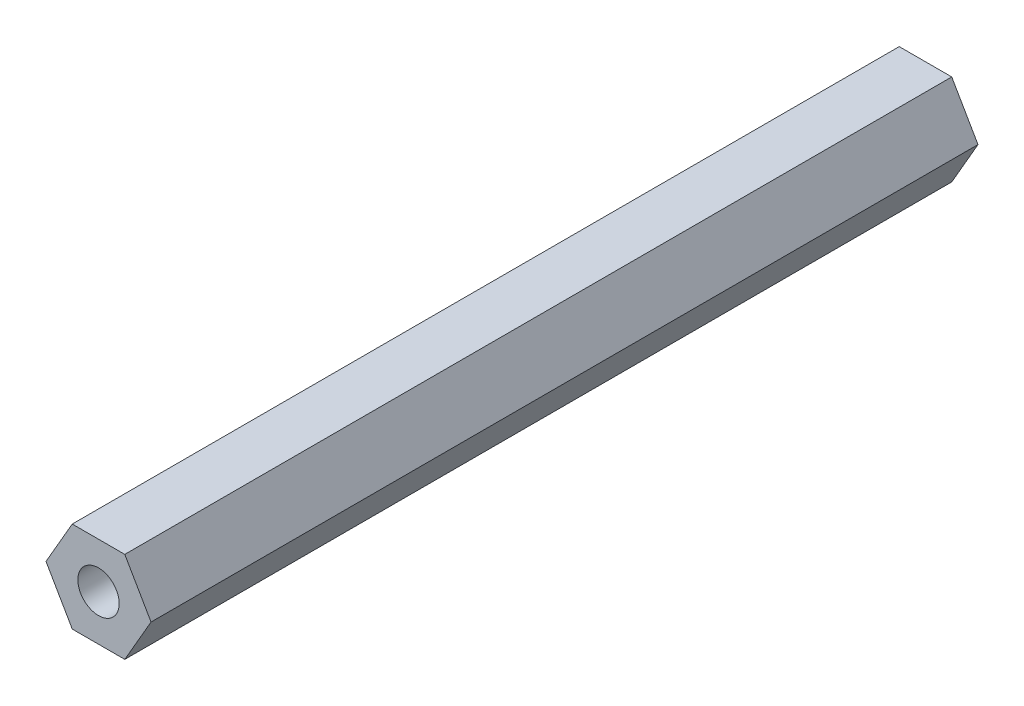
SolidWorks part; units mm, degrees
ref_plane "Front Plane" through (0, 0, 0) normal (0, 0, 1) x (1, 0, 0)
ref_plane "Top Plane" through (0, 0, 0) normal (0, 1, 0) x (1, 0, 0)
ref_plane "Right Plane" through (0, 0, 0) normal (1, 0, 0) x (0, 0, -1)
sketch "Sketch1" plane through (0, 0, 0) normal (0, 0, 1) x (1, 0, 0)
  line L1 (3.1754, 0) -> (1.5877, 2.75)
  line L2 (1.5877, 2.75) -> (-1.5877, 2.75)
  line L3 (-1.5877, 2.75) -> (-3.1754, 0)
  line L4 (-3.1754, 0) -> (-1.5877, -2.75)
  line L5 (-1.5877, -2.75) -> (1.5877, -2.75)
  line L6 (1.5877, -2.75) -> (3.1754, 0)
  circle A0 centre (0, 0) radius 2.75 construction
  dimension "D1" = 5.5
extrude "Boss-Extrude1" add sketch "Sketch1" along normal blind 50
sketch "Sketch3" plane through (0, 0, 50) normal (0, 0, 1) x (1, 0, 0)
  circle A0 centre (0, 0) radius 1.3122
hole_wizard "M3x0.5 Tapped Hole1" positions "3DSketch2" profile "Sketch4" tap size "M3x0.5" standard "ANSI Metric" end condition through all
sketch3d "3DSketch2"
  point P0 (0, 0, 50)
sketch "Sketch4" plane through (0, 0, 50) normal (1, 0, 0) x (0, -1, 0)
  line L0 (0, 0) -> (0, 50)
  line L1 (0, 50) -> (1.25, 50)
  line L2 (1.25, 50) -> (1.25, 0)
  line L5 (1.25, 0) -> (0, 0)
  line L11 (0, -6.35) -> (0, 107.95) construction
  dimension "Thru Tap Drill Dia." = 2.5
  dimension "Thru Tap Drill Depth" = 50
cosmetic thread "Hole Thread1" parameters "D2"=3
